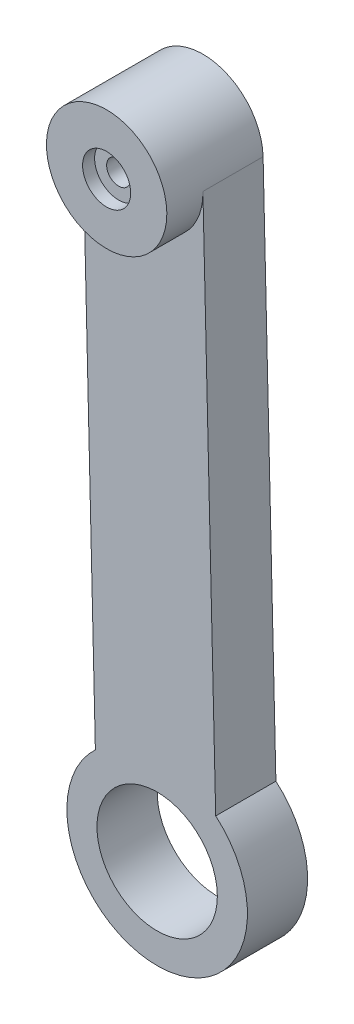
SolidWorks part; units mm, degrees
ref_plane "Front Plane" through (0, 0, 0) normal (0, 0, 1) x (1, 0, 0)
ref_plane "Top Plane" through (0, 0, 0) normal (0, 1, 0) x (1, 0, 0)
ref_plane "Right Plane" through (0, 0, 0) normal (1, 0, 0) x (0, 0, -1)
sketch "Sketch1" plane through (0, 0, 0) normal (0, 0, 1) x (0.9997, 0.0239, 0)
  line L0 (10.01, -0.02) -> (5.01, -0.02) construction
  line L1 (10.01, 49.98) -> (0.01, 49.98) construction
  line L2 (10.01, 49.98) -> (10.01, -0.02)
  line L3 (10.01, -0.02) -> (0.01, -0.02) construction
  line L4 (0.01, 49.98) -> (0.01, -0.02)
  line L6 (10.01, 24.98) -> (0.01, 24.98) construction
  circle A1 centre (5.01, 49.98) radius 2.4
  arc A2 (0.01, -0.02) -> (10.01, -0.02) centre (5.01, -0.02) ccw
  arc A3 (10.01, 49.98) -> (0.01, 49.98) centre (5.01, 49.98) ccw
  circle A4 centre (5.01, -0.02) radius 7.5
  circle A5 centre (5.01, -0.02) radius 5
  dimension "D1" = 4.8
  dimension "D4" = 15
  dimension "D6" = 10
  dimension "D2" = 50
  dimension "D3" = 10
  dimension "D5" = 50
extrude "Boss-Extrude1" add sketch "Sketch1" along normal blind 5
sketch "Sketch2" plane through (0, 0, 5) normal (0, 0, 1) x (1, 0, 0)
  circle A0 centre (3.8123, 50.0856) radius 5
  circle A1 centre (3.8123, 50.0856) radius 1
  dimension "D1" = 10
  dimension "D2" = 2
extrude "Boss-Extrude2" add sketch "Sketch2" along normal blind 3
sketch "Sketch3" plane through (0, 0, 8) normal (0, 0, 1) x (1, 0, 0)
  circle A0 centre (3.8123, 50.0856) radius 2
  dimension "D1" = 4
extrude "Cut-Extrude1" cut sketch "Sketch3" against normal offset from surface (1 mm away) 2 up to face at (4.452, 23.3658, 5)
move or copy body "Body-Move/Copy1" [suppressed] bodies to move or copy 101
